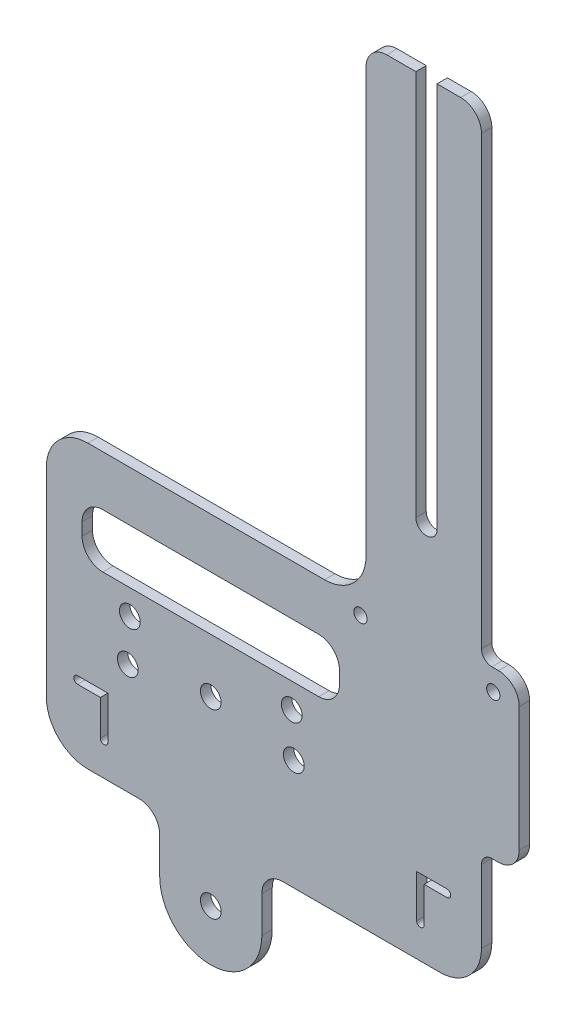
SolidWorks part; units mm, degrees
material "2024 Alloy"
ref_plane "Front Plane" through (0, 0, 0) normal (0, 0, 1) x (1, 0, 0)
ref_plane "Top Plane" through (0, 0, 0) normal (0, 1, 0) x (1, 0, 0)
ref_plane "Right Plane" through (0, 0, 0) normal (1, 0, 0) x (0, 0, -1)
sketch "Sketch1" plane through (0, 0, 0) normal (0, 0, 1) x (1, 0, 0)
  line L1 (-100, 150) -> (100, 150)
  line L2 (-100, 150) -> (-100, -150)
  line L3 (-100, -150) -> (100, -150)
  line L4 (100, 150) -> (100, -150)
  line L5 (-100, 150) -> (100, -150) construction
  line L6 (-100, -150) -> (100, 150) construction
  line L11 (100, 150) -> (3.7852, 150)
  line L12 (100, 150) -> (100, 170)
  line L13 (100, 170) -> (3.7852, 170)
  line L14 (3.7852, 150) -> (3.7852, 170)
  point P0 (0, 0)
  dimension "D1" = 300
  dimension "D2" = 200
  dimension "D3" = 20
extrude "Boss-Extrude1" add sketch "Sketch1" along normal blind 2.5 contours L4 L1 L2 L3 | L14 L1 L12 L13
sketch "Sketch2" plane through (0, 0, 2.5) normal (0, 0, 1) x (1, 0, 0)
  line L0 (44.5, 3.25) -> (37.2, 3.25)
  line L1 (-44.5, 23.75) -> (44.5, 23.75) construction
  line L2 (-44.5, 23.75) -> (-44.5, -23.75) construction
  line L3 (-44.5, -23.75) -> (44.5, -23.75) construction
  line L4 (44.5, 23.75) -> (44.5, -23.75) construction
  line L5 (-44.5, 23.75) -> (44.5, -23.75) construction
  line L6 (-44.5, -23.75) -> (44.5, 23.75) construction
  line L7 (37.2, 3.25) -> (37.2, -7.05)
  line L8 (37.2, -7.05) -> (39, -7.05)
  line L9 (39, -7.05) -> (39, 1.45)
  line L10 (39, 1.45) -> (44.5, 1.45)
  line L11 (44.5, 1.45) -> (44.5, 3.25)
  line L12 (0, -55) -> (0, 55) construction
  line L13 (-39, 1.45) -> (-44.5, 1.45)
  line L14 (-39, -7.05) -> (-39, 1.45)
  line L15 (-37.2, -7.05) -> (-39, -7.05)
  line L16 (-37.2, 3.25) -> (-37.2, -7.05)
  line L17 (-44.5, 3.25) -> (-37.2, 3.25)
  line L18 (-44.5, 1.45) -> (-44.5, 3.25)
  circle A0 centre (-32.4, 11.65) radius 4.6
  circle A1 centre (7.6, 11.65) radius 4.6
  circle A2 centre (-12.4, -28.75) radius 5
  circle A3 centre (-32.4, 11.65) radius 2.5
  circle A4 centre (7.6, 11.65) radius 2.5
  circle A5 centre (-12.4, -28.75) radius 2.5
  arc A6 (39, -7.05) -> (37.2, -7.05) centre (38.1, -7.05) cw
  arc A7 (44.5, 3.25) -> (44.5, 1.45) centre (44.5, 2.35) cw
  arc A8 (-44.5, 3.25) -> (-44.5, 1.45) centre (-44.5, 2.35) ccw
  arc A9 (-37.2, -7.05) -> (-39, -7.05) centre (-38.1, -7.05) cw
  point P0 (0, 0)
  dimension "D3" = 9.2
  dimension "D4" = 12.1
  dimension "D5" = 12.1
  dimension "D6" = 9.2
  dimension "D7" = 40
  dimension "D8" = 10
  dimension "D10" = 5
  dimension "D1" = 89
  dimension "D2" = 47.5
  dimension "D9" = 20
  dimension "D11" = 20.5
  dimension "D12" = 7.3
  dimension "D13" = 10.3
  dimension "D14" = 1.8
  dimension "D15" = 1.8
  dimension "D16" = 5
extrude "Cut-Extrude1" cut sketch "Sketch2" against normal blind 10 contours A5 | A4 | A3 | L18 L13 L14 L15 L16 L17 | L10 L11 L0 L7 L8 L9 | L18 A8 | A9 L15 | A6 L8 | A7 L11
sketch "Sketch4" plane through (0, 0, 2.5) normal (0, 0, 1) x (1, 0, 0)
  line L2 (37, 170) -> (37, 77)
  line L4 (52.8, 170) -> (25, 170)
  line L5 (42.1, 170) -> (42.1, 77)
  line L6 (100, 170) -> (3.7852, 170) construction
  line L7 (52.8, 170) -> (52.8, -15)
  line L8 (52.8, -15) -> (25.7244, -15)
  line L9 (-0.0958, -28.75) -> (-0.0958, -15)
  line L10 (-100, -150) -> (100, -150) construction
  line L11 (-24.7042, -28.75) -> (-24.7042, -15)
  line L12 (-24.7042, -15) -> (-52, -15)
  line L13 (-0.0958, -15) -> (25.7244, -15)
  line L18 (100, 170) -> (100, -150) construction
  line L20 (25, 53) -> (-52, 53)
  line L21 (-52, 53) -> (-52, -15)
  line L22 (-100, 150) -> (-100, -150) construction
  line L24 (52.8, 15) -> (61.9, 15)
  line L26 (25, 170) -> (25, 53)
  line L27 (52.8, 15) -> (52.8, 55)
  line L28 (52.8, 55) -> (61.9, 55)
  line L29 (61.9, 15) -> (61.9, 55)
  arc A2 (37, 77) -> (42.1, 77) centre (39.55, 77) ccw
  circle A3 centre (-12.4, -28.75) radius 12.3042
  dimension "D1" = 135
  dimension "D2" = 47.2
  dimension "D3" = 48
  dimension "D4" = 125
  dimension "D5" = 12
  dimension "D6" = 93
  dimension "D7" = 30
  dimension "D8" = 68
  dimension "D9" = 5.1
  dimension "D10" = 40
  dimension "D11" = 9.1
extrude "Cut-Extrude3" cut sketch "Sketch4" against normal blind 10
sketch "Sketch5" plane through (0, 0, 2.5) normal (0, 0, 1) x (1, 0, 0)
  line L0 (-43.4, 40.9093) -> (-43.4, 27.9093)
  line L1 (-12.4, 63.5894) -> (-12.4, 7.0443) construction
  line L3 (-43.4, 27.9093) -> (18.6, 27.9093)
  line L5 (18.6, 27.9093) -> (18.6, 40.9093)
  line L7 (18.6, 40.9093) -> (-43.4, 40.9093)
  circle A1 centre (-32.4, 11.65) radius 2.5 construction
  dimension "D3" = 20
  dimension "D1" = 13
  dimension "D2" = 62
extrude "Cut-Extrude4" cut sketch "Sketch5" against normal up to next
fillet "Fillet2" radius 5 4 edges at (18.6, 27.9093, 1.25) (-43.4, 27.9093, 1.25) (-43.4, 40.9093, 1.25) (18.6, 40.9093, 1.25)
fillet "Fillet3" radius 10 4 edges at (25, 53, 1.25) (-52, 53, 1.25) (52.8, -15, 1.25) (-52, -15, 1.25)
fillet "Fillet4" radius 5 6 edges at (-24.7042, -15, 1.25) (-0.0958, -15, 1.25) (25, 170, 1.25) (52.8, 170, 1.25) (61.9, 55, 1.25) (61.9, 15, 1.25)
sketch "Sketch7" plane through (0, 0, 2.5) normal (0, 0, 1) x (1, 0, 0)
  line L0 (61.9, 20) -> (61.9, 50) construction
  line L1 (52.8, 15) -> (56.9, 15) construction
  circle A0 centre (55.65, 49.91) radius 1.6
  circle A1 centre (23.65, 49.91) radius 1.6
  dimension "D1" = 3.2
  dimension "D2" = 6.25
  dimension "D3" = 32
  dimension "D4" = 34.91
extrude "Cut-Extrude6" cut sketch "Sketch7" against normal up to next
fillet "Fillet5" radius 2.5 2 edges at (52.8, 55, 1.25) (52.8, 15, 1.25)
sketch "Sketch8" plane through (0, 0, 2.5) normal (0, 0, 1) x (1, 0, 0)
  line L0 (-34.482, 21.9093) -> (10.8836, 21.9093) construction
  line L1 (-38.4, 27.9093) -> (13.6, 27.9093) construction
  line L2 (-12.4, -28.75) -> (-12.4, 23.6211) construction
  circle A0 centre (7.1, 21.9093) radius 2.5
  circle A1 centre (-31.9, 21.9093) radius 2.5
  circle A2 centre (-12.4, 14.9093) radius 2.5
  dimension "D2" = 5
  dimension "D1" = 6
  dimension "D3" = 19.5
  dimension "D4" = 7
extrude "Cut-Extrude7" cut sketch "Sketch8" against normal up to next
